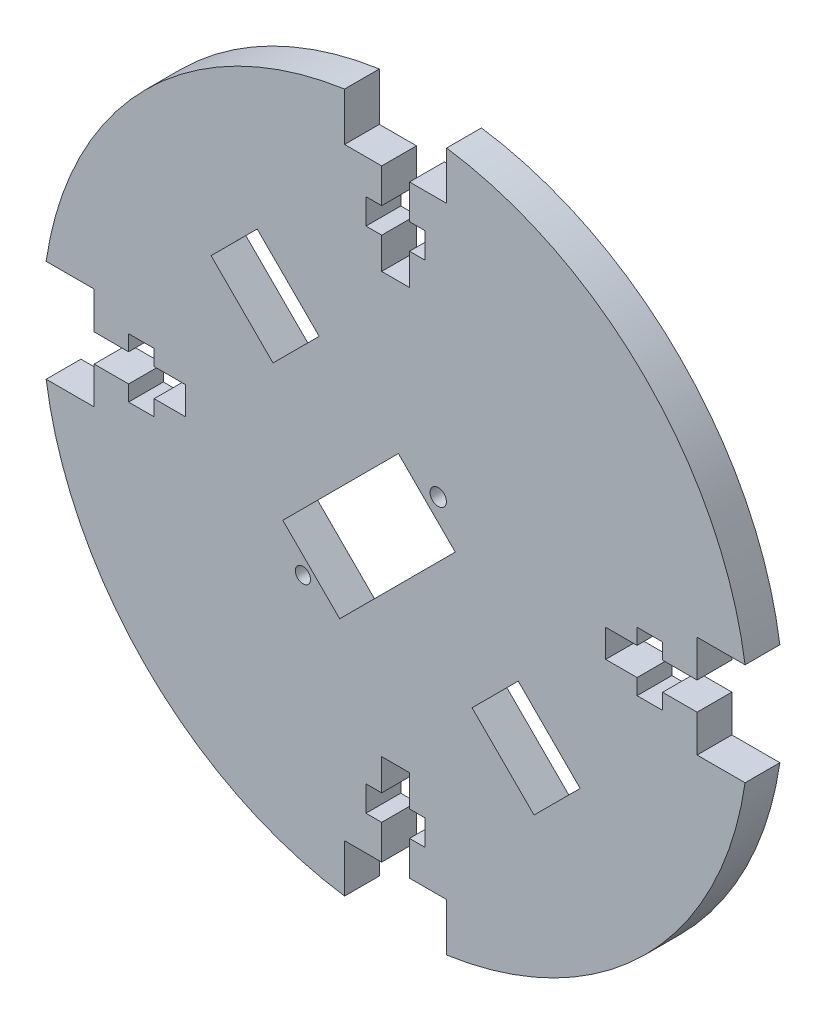
SolidWorks part; units mm, degrees
ref_plane "Front Plane" through (0, 0, 0) normal (0, 0, 1) x (1, 0, 0)
ref_plane "Top Plane" through (0, 0, 0) normal (0, 1, 0) x (1, 0, 0)
ref_plane "Right Plane" through (0, 0, 0) normal (1, 0, 0) x (0, 0, -1)
sketch "Sketch3" plane through (0, 0, 0) normal (0, 0, 1) x (1, 0, 0)
  line L28 (73.701, 59.6569) -> (14.8898, 59.6569) construction
  line L29 (81.0384, 102.9925) -> (81.0384, 109.8925)
  line L30 (75.701, 102.9925) -> (81.0384, 102.9925)
  line L31 (75.701, 98.0384) -> (75.701, 102.9925)
  line L32 (77.959, 98.0384) -> (75.701, 98.0384)
  line L33 (77.959, 94.3706) -> (77.959, 98.0384)
  line L34 (75.701, 94.3706) -> (77.959, 94.3706)
  line L35 (75.701, 89.854) -> (75.701, 94.3706)
  line L36 (71.701, 89.854) -> (71.701, 94.3706)
  line L37 (71.701, 94.3706) -> (69.443, 94.3706)
  line L38 (69.443, 94.3706) -> (69.443, 98.0384)
  line L39 (69.443, 98.0384) -> (71.701, 98.0384)
  line L40 (71.701, 98.0384) -> (71.701, 102.9925)
  line L41 (71.701, 102.9925) -> (66.3636, 102.9925)
  line L42 (66.3636, 102.9925) -> (66.3636, 109.8925)
  line L43 (117.0365, 66.9943) -> (123.9365, 66.9943)
  line L44 (103.8981, 61.6569) -> (108.4147, 61.6569)
  line L45 (108.4147, 61.6569) -> (108.4147, 63.9149)
  line L46 (108.4147, 63.9149) -> (112.0825, 63.9149)
  line L47 (112.0825, 63.9149) -> (112.0825, 61.6569)
  line L48 (112.0825, 61.6569) -> (117.0365, 61.6569)
  line L49 (117.0365, 61.6569) -> (117.0365, 66.9943)
  line L50 (108.4147, 61.6569) -> (108.4147, 63.9149)
  line L51 (108.4147, 63.9149) -> (112.0825, 63.9149)
  line L52 (112.0825, 63.9149) -> (112.0825, 61.6569)
  line L53 (112.0825, 61.6569) -> (117.0365, 61.6569)
  line L54 (117.0365, 61.6569) -> (117.0365, 66.9943)
  line L55 (108.4147, 61.6569) -> (108.4147, 63.9149)
  line L56 (108.4147, 63.9149) -> (112.0825, 63.9149)
  line L57 (112.0825, 63.9149) -> (112.0825, 61.6569)
  line L58 (81.0384, 102.9925) -> (81.0384, 109.8925)
  line L59 (75.701, 102.9925) -> (81.0384, 102.9925)
  line L60 (75.701, 98.0384) -> (75.701, 102.9925)
  line L61 (77.959, 98.0384) -> (75.701, 98.0384)
  line L62 (77.959, 94.3706) -> (77.959, 98.0384)
  line L63 (75.701, 94.3706) -> (77.959, 94.3706)
  line L64 (75.701, 89.854) -> (75.701, 94.3706)
  line L65 (75.701, 89.854) -> (71.701, 89.854)
  line L66 (71.701, 89.854) -> (71.701, 94.3706)
  line L67 (71.701, 94.3706) -> (69.443, 94.3706)
  line L68 (69.443, 94.3706) -> (69.443, 98.0384)
  line L69 (69.443, 98.0384) -> (71.701, 98.0384)
  line L70 (71.701, 98.0384) -> (71.701, 102.9925)
  line L71 (71.701, 102.9925) -> (66.3636, 102.9925)
  line L72 (66.3636, 102.9925) -> (66.3636, 109.8925)
  line L73 (30.3655, 66.9943) -> (23.4655, 66.9943)
  line L74 (30.3655, 52.3196) -> (23.4655, 52.3196)
  line L75 (43.5039, 57.6569) -> (38.9873, 57.6569)
  line L76 (30.3655, 61.6569) -> (30.3655, 66.9943)
  line L77 (35.3195, 61.6569) -> (30.3655, 61.6569)
  line L78 (35.3195, 63.9149) -> (35.3195, 61.6569)
  line L79 (38.9873, 63.9149) -> (35.3195, 63.9149)
  line L80 (38.9873, 61.6569) -> (38.9873, 63.9149)
  line L81 (43.5039, 61.6569) -> (38.9873, 61.6569)
  line L82 (30.3655, 61.6569) -> (30.3655, 66.9943)
  line L83 (35.3195, 61.6569) -> (30.3655, 61.6569)
  line L84 (35.3195, 63.9149) -> (35.3195, 61.6569)
  line L85 (38.9873, 63.9149) -> (35.3195, 63.9149)
  line L86 (38.9873, 61.6569) -> (38.9873, 63.9149)
  line L87 (43.5039, 61.6569) -> (38.9873, 61.6569)
  line L88 (57.4878, 51.7692) -> (74.0999, 68.3816)
  line L89 (57.4878, 51.7692) -> (65.663, 43.5941)
  line L90 (74.0999, 68.3816) -> (82.2751, 60.2065)
  line L91 (65.663, 43.5941) -> (82.2751, 60.2065)
  line L92 (47.1726, 79.5532) -> (53.8046, 86.186)
  line L93 (47.1726, 79.5532) -> (56.0787, 70.6482)
  line L94 (53.8046, 86.186) -> (62.7107, 77.281)
  line L95 (56.0787, 70.6482) -> (62.7107, 77.281)
  line L96 (73.701, 59.6569) -> (73.701, 0) construction
  line L97 (73.701, 0) -> (0, 0) construction
  line L99 (73.701, 59.6569) -> (73.701, 117.1033) construction
  line L101 (81.0384, 102.9925) -> (81.0384, 109.8925)
  line L102 (75.701, 102.9925) -> (81.0384, 102.9925)
  line L103 (75.701, 98.0384) -> (75.701, 102.9925)
  line L104 (77.959, 98.0384) -> (75.701, 98.0384)
  line L105 (77.959, 94.3706) -> (77.959, 98.0384)
  line L106 (75.701, 94.3706) -> (77.959, 94.3706)
  line L107 (75.701, 89.854) -> (75.701, 94.3706)
  line L108 (71.701, 89.854) -> (71.701, 94.3706)
  line L109 (71.701, 94.3706) -> (69.443, 94.3706)
  line L110 (69.443, 94.3706) -> (69.443, 98.0384)
  line L111 (69.443, 98.0384) -> (71.701, 98.0384)
  line L112 (71.701, 98.0384) -> (71.701, 102.9925)
  line L113 (71.701, 102.9925) -> (66.3636, 102.9925)
  line L114 (66.3636, 102.9925) -> (66.3636, 109.8925)
  line L115 (81.0384, 102.9925) -> (81.0384, 109.8925)
  line L116 (75.701, 102.9925) -> (81.0384, 102.9925)
  line L117 (75.701, 98.0384) -> (75.701, 102.9925)
  line L118 (77.959, 98.0384) -> (75.701, 98.0384)
  line L119 (77.959, 94.3706) -> (77.959, 98.0384)
  line L120 (75.701, 94.3706) -> (77.959, 94.3706)
  line L121 (75.701, 89.854) -> (75.701, 94.3706)
  line L122 (71.701, 89.854) -> (71.701, 94.3706)
  line L123 (71.701, 94.3706) -> (69.443, 94.3706)
  line L124 (69.443, 94.3706) -> (69.443, 98.0384)
  line L125 (69.443, 98.0384) -> (71.701, 98.0384)
  line L126 (71.701, 98.0384) -> (71.701, 102.9925)
  line L127 (71.701, 102.9925) -> (66.3636, 102.9925)
  line L128 (66.3636, 102.9925) -> (66.3636, 109.8925)
  line L129 (66.3636, 16.3214) -> (66.3636, 9.4214)
  line L130 (71.701, 16.3214) -> (66.3636, 16.3214)
  line L131 (71.701, 21.2755) -> (71.701, 16.3214)
  line L132 (69.443, 21.2755) -> (71.701, 21.2755)
  line L133 (69.443, 24.9433) -> (69.443, 21.2755)
  line L134 (71.701, 24.9433) -> (69.443, 24.9433)
  line L135 (71.701, 16.3214) -> (66.3636, 16.3214)
  line L136 (71.701, 21.2755) -> (71.701, 16.3214)
  line L137 (69.443, 21.2755) -> (71.701, 21.2755)
  line L138 (69.443, 24.9433) -> (69.443, 21.2755)
  line L139 (71.701, 24.9433) -> (69.443, 24.9433)
  line L140 (71.701, 16.3214) -> (66.3636, 16.3214)
  line L141 (71.701, 21.2755) -> (71.701, 16.3214)
  line L142 (69.443, 21.2755) -> (71.701, 21.2755)
  line L143 (69.443, 24.9433) -> (69.443, 21.2755)
  line L144 (71.701, 24.9433) -> (69.443, 24.9433)
  line L145 (71.701, 16.3214) -> (66.3636, 16.3214)
  line L146 (71.701, 21.2755) -> (71.701, 16.3214)
  line L147 (69.443, 21.2755) -> (71.701, 21.2755)
  line L148 (69.443, 24.9433) -> (69.443, 21.2755)
  line L149 (71.701, 24.9433) -> (69.443, 24.9433)
  line L150 (75.701, 29.4599) -> (75.701, 24.9433)
  line L151 (75.701, 24.9433) -> (77.959, 24.9433)
  line L152 (77.959, 24.9433) -> (77.959, 21.2755)
  line L153 (77.959, 21.2755) -> (75.701, 21.2755)
  line L154 (75.701, 21.2755) -> (75.701, 16.3214)
  line L155 (75.701, 16.3214) -> (81.0384, 16.3214)
  line L156 (81.0384, 16.3214) -> (81.0384, 9.4214)
  line L157 (75.701, 29.4599) -> (75.701, 24.9433)
  line L158 (75.701, 24.9433) -> (77.959, 24.9433)
  line L159 (77.959, 24.9433) -> (77.959, 21.2755)
  line L160 (77.959, 21.2755) -> (75.701, 21.2755)
  line L161 (75.701, 21.2755) -> (75.701, 16.3214)
  line L162 (75.701, 16.3214) -> (81.0384, 16.3214)
  line L163 (81.0384, 16.3214) -> (81.0384, 9.4214)
  line L164 (75.701, 29.4599) -> (71.701, 29.4599)
  line L165 (75.701, 29.4599) -> (75.701, 24.9433)
  line L166 (75.701, 24.9433) -> (77.959, 24.9433)
  line L167 (77.959, 24.9433) -> (77.959, 21.2755)
  line L168 (77.959, 21.2755) -> (75.701, 21.2755)
  line L169 (75.701, 21.2755) -> (75.701, 16.3214)
  line L170 (75.701, 16.3214) -> (81.0384, 16.3214)
  line L171 (81.0384, 16.3214) -> (81.0384, 9.4214)
  line L172 (75.701, 29.4599) -> (75.701, 24.9433)
  line L173 (75.701, 24.9433) -> (77.959, 24.9433)
  line L174 (77.959, 24.9433) -> (77.959, 21.2755)
  line L175 (77.959, 21.2755) -> (75.701, 21.2755)
  line L176 (75.701, 21.2755) -> (75.701, 16.3214)
  line L177 (75.701, 16.3214) -> (81.0384, 16.3214)
  line L178 (81.0384, 16.3214) -> (81.0384, 9.4214)
  line L179 (71.701, 29.4599) -> (71.701, 24.9433)
  line L180 (73.701, 59.6569) -> (25.764, 11.7199) construction
  line L181 (43.5039, 61.6569) -> (43.5039, 57.6569)
  line L182 (30.3655, 61.6569) -> (30.3655, 66.9943)
  line L183 (35.3195, 61.6569) -> (30.3655, 61.6569)
  line L184 (35.3195, 63.9149) -> (35.3195, 61.6569)
  line L185 (38.9873, 63.9149) -> (35.3195, 63.9149)
  line L186 (38.9873, 61.6569) -> (38.9873, 63.9149)
  line L187 (43.5039, 61.6569) -> (38.9873, 61.6569)
  line L188 (30.3655, 61.6569) -> (30.3655, 66.9943)
  line L189 (35.3195, 61.6569) -> (30.3655, 61.6569)
  line L190 (35.3195, 63.9149) -> (35.3195, 61.6569)
  line L191 (38.9873, 63.9149) -> (35.3195, 63.9149)
  line L192 (38.9873, 61.6569) -> (38.9873, 63.9149)
  line L193 (43.5039, 61.6569) -> (38.9873, 61.6569)
  line L194 (38.9873, 57.6569) -> (38.9873, 55.3989)
  line L195 (38.9873, 55.3989) -> (35.3195, 55.3989)
  line L196 (35.3195, 55.3989) -> (35.3195, 57.6569)
  line L197 (35.3195, 57.6569) -> (30.3655, 57.6569)
  line L198 (30.3655, 57.6569) -> (30.3655, 52.3196)
  line L199 (38.9873, 57.6569) -> (38.9873, 55.3989)
  line L200 (38.9873, 55.3989) -> (35.3195, 55.3989)
  line L201 (35.3195, 55.3989) -> (35.3195, 57.6569)
  line L202 (35.3195, 57.6569) -> (30.3655, 57.6569)
  line L203 (30.3655, 57.6569) -> (30.3655, 52.3196)
  line L204 (38.9873, 57.6569) -> (38.9873, 55.3989)
  line L205 (38.9873, 55.3989) -> (35.3195, 55.3989)
  line L206 (35.3195, 55.3989) -> (35.3195, 57.6569)
  line L207 (35.3195, 57.6569) -> (30.3655, 57.6569)
  line L208 (30.3655, 57.6569) -> (30.3655, 52.3196)
  line L209 (38.9873, 57.6569) -> (38.9873, 55.3989)
  line L210 (38.9873, 55.3989) -> (35.3195, 55.3989)
  line L211 (35.3195, 55.3989) -> (35.3195, 57.6569)
  line L212 (35.3195, 57.6569) -> (30.3655, 57.6569)
  line L213 (30.3655, 57.6569) -> (30.3655, 52.3196)
  line L214 (112.0825, 61.6569) -> (117.0365, 61.6569)
  line L215 (117.0365, 61.6569) -> (117.0365, 66.9943)
  line L216 (108.4147, 61.6569) -> (108.4147, 63.9149)
  line L217 (108.4147, 63.9149) -> (112.0825, 63.9149)
  line L218 (112.0825, 63.9149) -> (112.0825, 61.6569)
  line L219 (112.0825, 61.6569) -> (117.0365, 61.6569)
  line L220 (117.0365, 61.6569) -> (117.0365, 66.9943)
  line L221 (117.0365, 57.6569) -> (117.0365, 52.3196)
  line L222 (112.0825, 57.6569) -> (117.0365, 57.6569)
  line L223 (112.0825, 55.3989) -> (112.0825, 57.6569)
  line L224 (108.4147, 55.3989) -> (112.0825, 55.3989)
  line L225 (108.4147, 57.6569) -> (108.4147, 55.3989)
  line L226 (117.0365, 57.6569) -> (117.0365, 52.3196)
  line L227 (112.0825, 57.6569) -> (117.0365, 57.6569)
  line L228 (112.0825, 55.3989) -> (112.0825, 57.6569)
  line L229 (108.4147, 55.3989) -> (112.0825, 55.3989)
  line L230 (108.4147, 57.6569) -> (108.4147, 55.3989)
  line L231 (117.0365, 57.6569) -> (117.0365, 52.3196)
  line L232 (112.0825, 57.6569) -> (117.0365, 57.6569)
  line L233 (112.0825, 55.3989) -> (112.0825, 57.6569)
  line L234 (108.4147, 55.3989) -> (112.0825, 55.3989)
  line L235 (108.4147, 57.6569) -> (108.4147, 55.3989)
  line L236 (117.0365, 57.6569) -> (117.0365, 52.3196)
  line L237 (112.0825, 57.6569) -> (117.0365, 57.6569)
  line L238 (112.0825, 55.3989) -> (112.0825, 57.6569)
  line L239 (108.4147, 55.3989) -> (112.0825, 55.3989)
  line L240 (108.4147, 57.6569) -> (108.4147, 55.3989)
  line L241 (103.8981, 61.6569) -> (103.8981, 57.6569)
  line L242 (103.8981, 57.6569) -> (108.4147, 57.6569)
  line L243 (117.0365, 52.3196) -> (123.9365, 52.3196)
  line L244 (84.6923, 42.0346) -> (91.3251, 48.6666)
  line L245 (93.5973, 33.1286) -> (84.6923, 42.0346)
  line L246 (100.2301, 39.7606) -> (91.3251, 48.6666)
  line L247 (93.5973, 33.1286) -> (100.2301, 39.7606)
  circle A10 centre (60.3822, 46.3931) radius 1.0891
  circle A11 centre (79.8275, 65.8387) radius 1.1751
  circle A17 centre (73.701, 59.6569) radius 50.7685
  arc A18 (80.2157, 67.2876) -> (81.2764, 66.2269) centre (79.8275, 65.8387) ccw construction
  point P62 (51.6257, 75.1007)
  point P65 (89.1448, 37.5816)
  dimension "D1" = 73.701
  dimension "D2" = 59.6569
  dimension "D3" = 101.5371
  dimension "D4" = 7.3374
  dimension "D5" = 20.0384
  dimension "D6" = 4.5166
  dimension "D7" = 2
  dimension "D8" = 3.6678
  dimension "D9" = 4.258
  dimension "D10" = 6.9
  dimension "D11" = 45
extrude "Boss-Extrude5" add sketch "Sketch3" along normal blind 5 separate body
